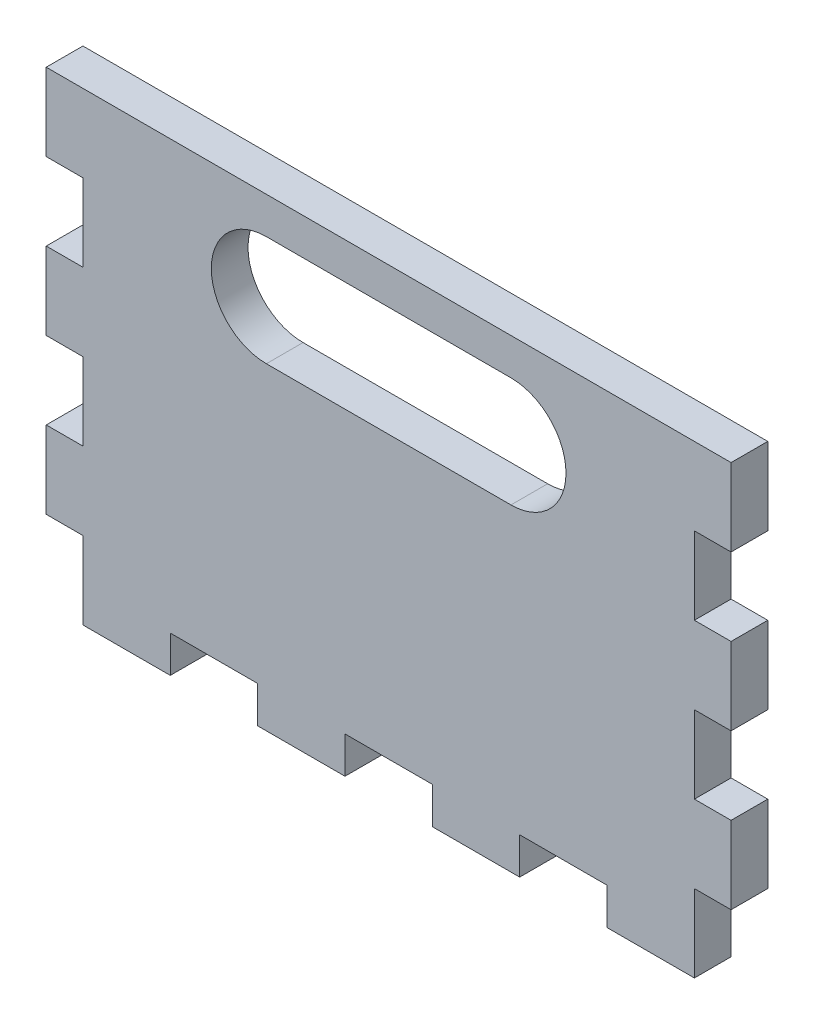
SolidWorks part; units mm, degrees
material "Pino"
ref_plane "Piano frontale" through (0, 0, 0) normal (0, 0, 1) x (1, 0, 0)
ref_plane "Piano superiore" through (0, 0, 0) normal (0, 1, 0) x (1, 0, 0)
ref_plane "Piano destro" through (0, 0, 0) normal (1, 0, 0) x (0, 0, -1)
sketch "Schizzo1" plane through (0, 0, 0) normal (0, 0, 1) x (1, 0, 0)
  line L0 (25, 17.5) -> (28, 17.5)
  line L1 (-25, -17.5) -> (25, -17.5) construction
  line L2 (-25, -20.5) -> (-25, -14.1667)
  line L3 (-25, 17.5) -> (25, 17.5)
  line L4 (25, 11.1667) -> (25, 4.8333)
  line L5 (-25, -17.5) -> (25, 17.5) construction
  line L6 (-25, 17.5) -> (25, -17.5) construction
  line L7 (28, 17.5) -> (28, 11.1667)
  line L8 (25, 4.8333) -> (28, 4.8333)
  line L9 (25, 11.1667) -> (28, 11.1667)
  line L10 (28, 4.8333) -> (28, -1.5)
  line L11 (28, -1.5) -> (25, -1.5)
  line L12 (0, 17.5) -> (0, -17.5) construction
  line L13 (25, -1.5) -> (25, -7.8333)
  line L14 (-28, -14.1667) -> (-25, -14.1667)
  line L15 (25, -7.8333) -> (28, -7.8333)
  line L16 (28, -7.8333) -> (28, -14.1667)
  line L17 (28, -14.1667) -> (25, -14.1667)
  line L18 (25, -20.5) -> (25, -14.1667)
  line L19 (-25, -20.5) -> (-17.8571, -20.5)
  line L20 (-17.8571, -20.5) -> (-17.8571, -17.5)
  line L21 (-17.8571, -17.5) -> (-10.7143, -17.5)
  line L22 (-10.7143, -17.5) -> (-10.7143, -20.5)
  line L23 (-28, -7.8333) -> (-28, -14.1667)
  line L24 (-25, -7.8333) -> (-28, -7.8333)
  line L25 (-25, -1.5) -> (-25, -7.8333)
  line L26 (-28, -1.5) -> (-25, -1.5)
  line L27 (-28, 4.8333) -> (-28, -1.5)
  line L28 (-25, 11.1667) -> (-28, 11.1667)
  line L29 (-25, 4.8333) -> (-28, 4.8333)
  line L30 (-28, 17.5) -> (-28, 11.1667)
  line L31 (-25, 11.1667) -> (-25, 4.8333)
  line L32 (-25, 17.5) -> (-28, 17.5)
  line L33 (-10.7143, -20.5) -> (-3.5714, -20.5)
  line L34 (-3.5714, -20.5) -> (-3.5714, -17.5)
  line L35 (-3.5714, -17.5) -> (3.5714, -17.5)
  line L36 (3.5714, -17.5) -> (3.5714, -20.5)
  line L37 (3.5714, -20.5) -> (10.7143, -20.5)
  line L38 (10.7143, -20.5) -> (10.7143, -17.5)
  line L39 (10.7143, -17.5) -> (17.8571, -17.5)
  line L40 (17.8571, -17.5) -> (17.8571, -20.5)
  line L41 (17.8571, -20.5) -> (25, -20.5)
  line L42 (-10, 10) -> (10, 10) construction
  line L43 (-25, 17.5) -> (-25, -17.5) construction
  line L44 (25, 17.5) -> (25, -17.5) construction
  line L45 (-10, 14.5) -> (10, 14.5)
  line L46 (-10, 5.5) -> (10, 5.5)
  arc A0 (-10, 14.5) -> (-10, 5.5) centre (-10, 10) ccw
  arc A1 (10, 5.5) -> (10, 14.5) centre (10, 10) ccw
  point P0 (0, 0)
  point P46 (0, 10)
  dimension "D3" = 3
  dimension "D1" = 50
  dimension "D2" = 35
  dimension "D4" = 3
extrude "Estrusione-Estrusione1" add sketch "Schizzo1" along normal mid plane 3
